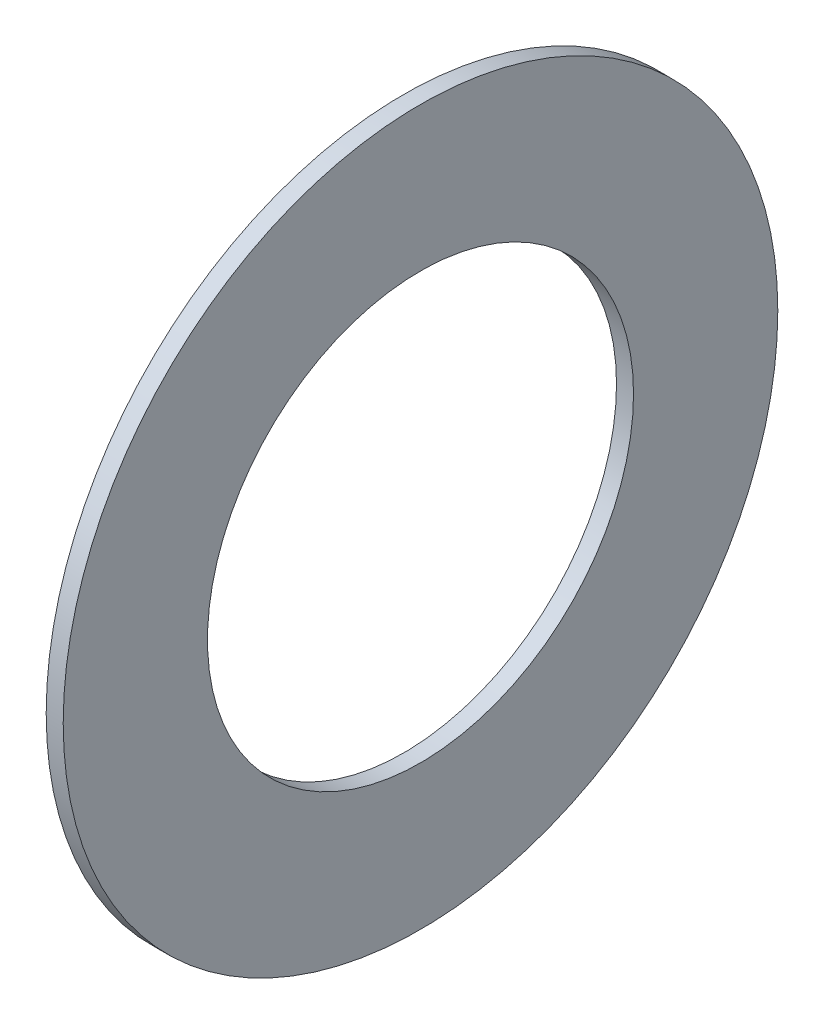
SolidWorks part; units mm, degrees
ref_plane "Front Plane" through (0, 0, 0) normal (0, 0, 1) x (1, 0, 0)
ref_plane "Top Plane" through (0, 0, 0) normal (0, 1, 0) x (1, 0, 0)
ref_plane "Right Plane" through (0, 0, 0) normal (1, 0, 0) x (0, 0, -1)
sketch "Sketch1" plane through (0, 0, 0) normal (1, 0, 0) x (0, 0, -1)
  circle A0 centre (0, 0) radius 21
  circle A1 centre (0, 0) radius 12.5 construction
  circle A2 centre (0, 0) radius 12.52
  dimension "OD" = 42
  dimension "For Shaft Diameter" = 25
  dimension "ID" = 25.04
sketch "Sketch2" plane through (0, 0, 0) normal (0, 0, 1) x (1, 0, 0)
  line L0 (0.5, 0) -> (-0.5, 0) construction
  line L1 (0.5, -21) -> (-0.5, -21) construction
  line L2 (0.5, -21) -> (0.5, 21) construction
  line L3 (0.5, 21) -> (-0.5, 21) construction
  line L4 (-0.5, -21) -> (-0.5, 21) construction
  point P6 (0, 21)
  point P9 (0, -21)
  dimension "Thickness" = 1
sketch "Sketch3" plane through (0, 0, 0) normal (1, 0, 0) x (0, 0, -1)
  circle A1 centre (0, 0) radius 21 construction
  circle A3 centre (0, 0) radius 21
  circle A4 centre (0, 0) radius 12.52 construction
  circle A5 centre (0, 0) radius 12.52
extrude "Boss-Extrude1" add sketch "Sketch3" along normal up to vertex (0.5 mm away) and the other way up to vertex (0.5 mm away) up to point (0.5, 21, 0) other way up to point (-0.5, 21, 0)
